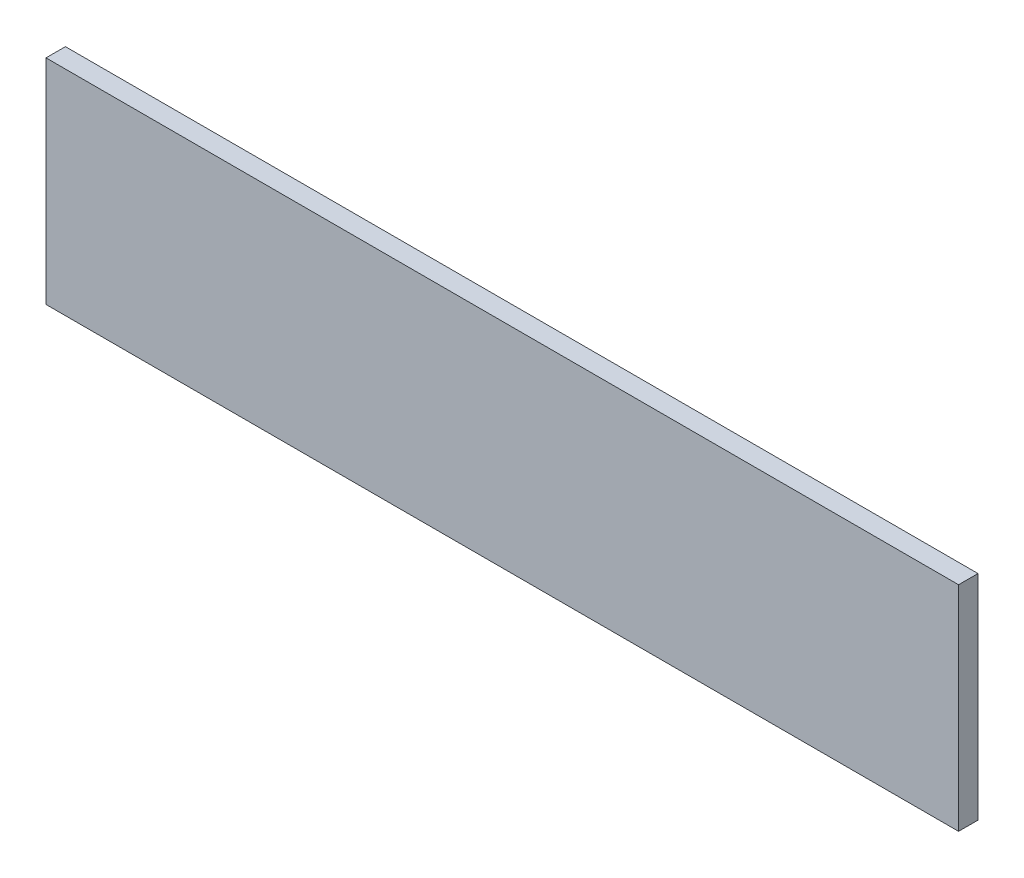
SolidWorks part; units mm, degrees
ref_plane "Plan de face" through (0, 0, 0) normal (0, 0, 1) x (1, 0, 0)
ref_plane "Plan de dessus" through (0, 0, 0) normal (0, 1, 0) x (1, 0, 0)
ref_plane "Plan de droite" through (0, 0, 0) normal (1, 0, 0) x (0, 0, -1)
sketch "Esquisse1" plane through (0, 0, 0) normal (0, 0, 1) x (1, 0, 0)
  line L1 (470, 110) -> (0, 110)
  line L2 (470, 110) -> (470, 0)
  line L3 (470, 0) -> (0, 0)
  line L4 (0, 110) -> (0, 0)
  dimension "D1" = 470
  dimension "D2" = 110
extrude "Boss.-Extru.1" add sketch "Esquisse1" along normal blind 10
